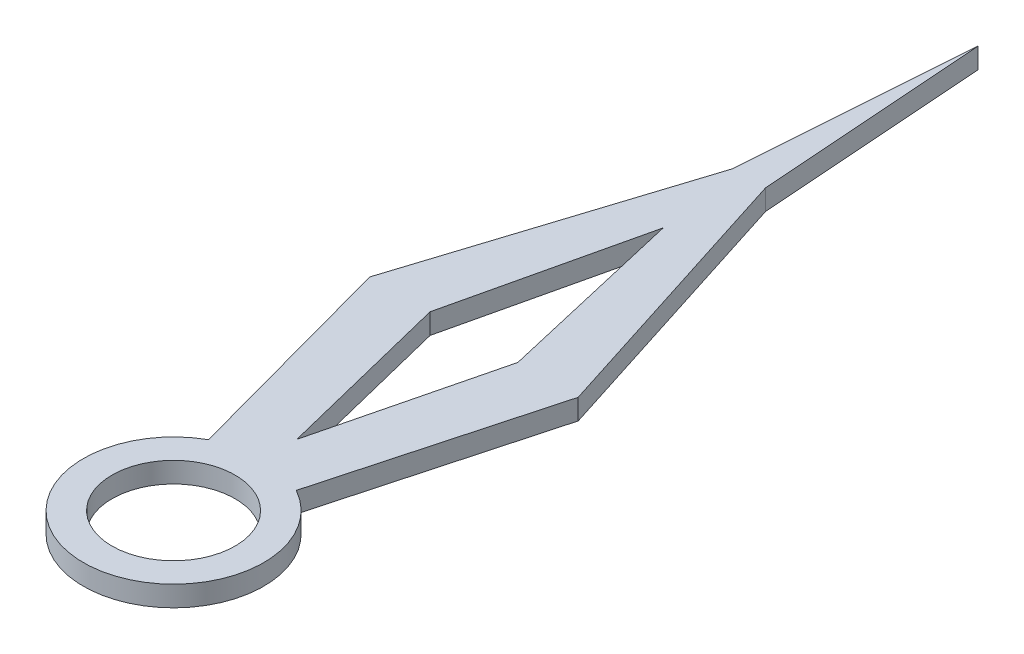
SolidWorks part; units mm, degrees
ref_plane "Front Plane" through (0, 0, 0) normal (0, 0, 1) x (1, 0, 0)
ref_plane "Top Plane" through (0, 0, 0) normal (0, 1, 0) x (1, 0, 0)
ref_plane "Right Plane" through (0, 0, 0) normal (1, 0, 0) x (0, 0, -1)
sketch "Sketch1" plane through (0, 0, 0) normal (0, 1, 0) x (1, 0, 0)
  line L0 (0, 456.7334) -> (0, -113.4441) construction
  line L1 (-21.3919, 38.4222) -> (-50.8101, 146.4582)
  line L2 (-50.8101, 146.4582) -> (-8.048, 280.5663)
  line L3 (-132.885, 392.1832) -> (132.885, 392.1832) construction
  line L4 (-8.048, 280.5663) -> (0, 392.1832)
  line L5 (21.3919, 38.4222) -> (50.8101, 146.4582)
  line L6 (8.048, 280.5663) -> (0, 392.1832)
  line L7 (50.8101, 146.4582) -> (8.048, 280.5663)
  line L8 (0, 238.7382) -> (-21.3919, 146.4582)
  line L9 (-21.3919, 146.4582) -> (0, 60.0777)
  line L10 (21.3919, 146.4582) -> (0, 60.0777)
  line L11 (0, 238.7382) -> (21.3919, 146.4582)
  circle A0 centre (0, 0) radius 30
  arc A1 (-21.3919, 38.4222) -> (21.3919, 38.4222) centre (0, 0) ccw
  point P6 (-8.048, 280.5663)
  point P13 (0, 392.1832)
  point P20 (21.8558, 38.0614)
  point P21 (0, 238.7382)
  point P22 (-21.3919, 146.4582)
  point P23 (-50.8101, 146.4582)
extrude "Boss-Extrude1" add sketch "Sketch1" along normal blind 10
